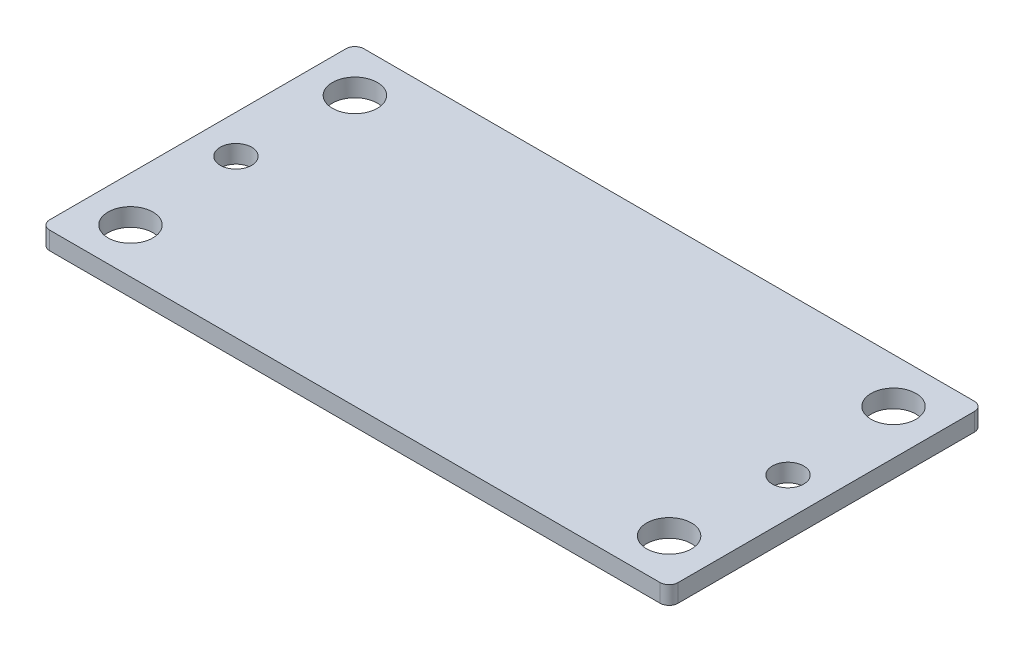
SolidWorks part; units mm, degrees
material "Plain Carbon Steel"
ref_plane "Front Plane" through (0, 0, 0) normal (0, 0, 1) x (1, 0, 0)
ref_plane "Top Plane" through (0, 0, 0) normal (0, 1, 0) x (1, 0, 0)
ref_plane "Right Plane" through (0, 0, 0) normal (1, 0, 0) x (0, 0, -1)
sketch "Sketch1" plane through (0, 0, 0) normal (0, 1, 0) x (1, 0, 0)
  line L1 (0, 0) -> (70, 0)
  line L2 (0, 0) -> (0, 35)
  line L3 (0, 35) -> (70, 35)
  line L4 (70, 0) -> (70, 35)
  dimension "D1" = 70
  dimension "D2" = 35
extrude "Boss-Extrude1" add sketch "Sketch1" along normal blind 2
sketch "Sketch2" plane through (0, 2, 0) normal (0, 1, 0) x (1, 0, 0)
  line L0 (0, 35) -> (0, 0) construction
  line L1 (5, 30) -> (5, 35) construction
  line L2 (70, 35) -> (0, 35) construction
  line L3 (5, 30) -> (0, 30) construction
  line L4 (2.5, 30) -> (2.5, 5) construction
  line L5 (5, 5) -> (0, 5) construction
  line L6 (5, 5) -> (5, 0) construction
  line L7 (0, 0) -> (70, 0) construction
  line L8 (4.25, 17.5) -> (0, 17.5) construction
  line L9 (35, 35) -> (35, 0) construction
  line L10 (65.75, 17.5) -> (70, 17.5) construction
  line L11 (65, 5) -> (65, 0) construction
  line L12 (65, 5) -> (70, 5) construction
  line L13 (67.5, 30) -> (67.5, 5) construction
  line L14 (65, 30) -> (70, 30) construction
  line L15 (65, 30) -> (65, 35) construction
  circle A0 centre (5, 30) radius 2.5
  circle A1 centre (5, 5) radius 2.5
  circle A2 centre (4.25, 17.5) radius 1.75
  circle A3 centre (65.75, 17.5) radius 1.75
  circle A4 centre (65, 5) radius 2.5
  circle A5 centre (65, 30) radius 2.5
  dimension "D2" = 5
  dimension "D3" = 3.5
  dimension "D1" = 5
extrude "Cut-Extrude1" cut sketch "Sketch2" against normal through all both and the other way through all
fillet "Fillet1" radius 1 4 edges at (0, 1, -35) (0, 1, 0) (70, 1, 0) (70, 1, -35)
